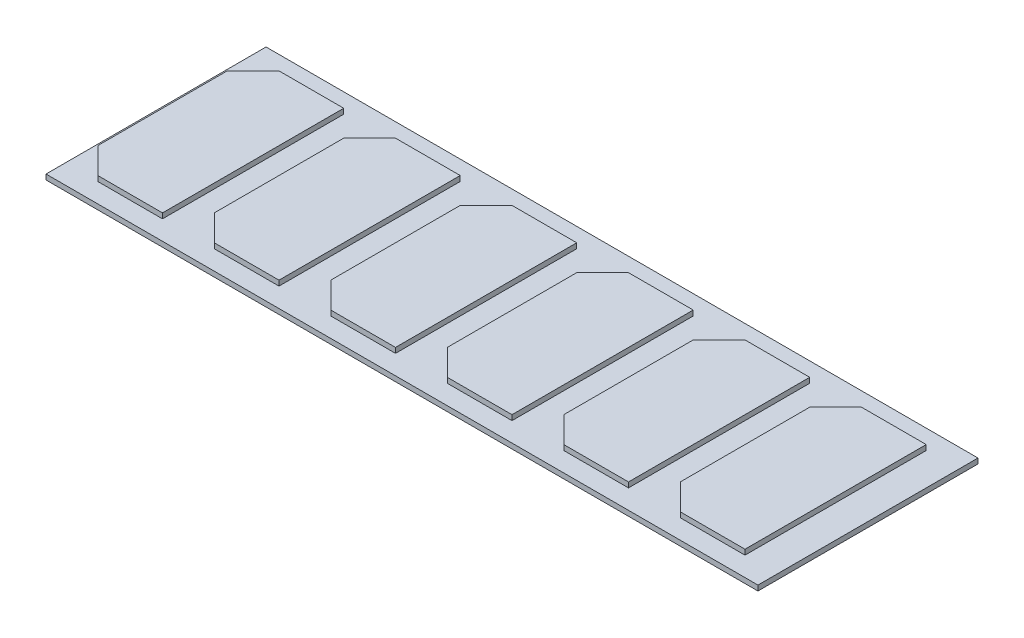
SolidWorks part; units mm, degrees
ref_plane "Front Plane" through (0, 0, 0) normal (0, 0, 1) x (1, 0, 0)
ref_plane "Top Plane" through (0, 0, 0) normal (0, 1, 0) x (1, 0, 0)
ref_plane "Right Plane" through (0, 0, 0) normal (1, 0, 0) x (0, 0, -1)
sketch "Sketch1" plane through (0, 0, 0) normal (0, 1, 0) x (1, 0, 0)
  line L1 (-137.5, -42.5) -> (137.5, -42.5)
  line L2 (-137.5, -42.5) -> (-137.5, 42.5)
  line L3 (-137.5, 42.5) -> (137.5, 42.5)
  line L4 (137.5, -42.5) -> (137.5, 42.5)
  line L5 (-137.5, -42.5) -> (137.5, 42.5) construction
  line L6 (-137.5, 42.5) -> (137.5, -42.5) construction
  point P0 (0, 0)
  dimension "D1" = 275
  dimension "D2" = 85
extrude "Boss-Extrude1" add sketch "Sketch1" along normal blind 2
sketch "Sketch2" plane through (0, 2, 0) normal (0, 1, 0) x (1, 0, 0)
  line L0 (-100, 35) -> (-100, -35)
  line L1 (-100, -35) -> (-125, -35)
  line L2 (-125, -35) -> (-135, -25)
  line L3 (-135, -25) -> (-135, 25)
  line L4 (-135, 25) -> (-125, 35)
  line L5 (-125, 35) -> (-100, 35)
  line L6 (-186.987, 0) -> (-73.9541, 0) construction
  line L7 (-90, 25) -> (-80, 35)
  line L8 (-90, -25) -> (-90, 25)
  line L9 (-80, -35) -> (-90, -25)
  line L10 (-55, -35) -> (-80, -35)
  line L11 (-55, 35) -> (-55, -35)
  line L12 (-80, 35) -> (-55, 35)
  line L13 (-45, 25) -> (-35, 35)
  line L14 (-45, -25) -> (-45, 25)
  line L15 (-35, -35) -> (-45, -25)
  line L16 (-10, -35) -> (-35, -35)
  line L17 (-10, 35) -> (-10, -35)
  line L18 (-35, 35) -> (-10, 35)
  line L19 (0, 25) -> (10, 35)
  line L20 (0, -25) -> (0, 25)
  line L21 (10, -35) -> (0, -25)
  line L22 (35, -35) -> (10, -35)
  line L23 (35, 35) -> (35, -35)
  line L24 (10, 35) -> (35, 35)
  line L25 (45, 25) -> (55, 35)
  line L26 (45, -25) -> (45, 25)
  line L27 (55, -35) -> (45, -25)
  line L28 (80, -35) -> (55, -35)
  line L29 (80, 35) -> (80, -35)
  line L30 (55, 35) -> (80, 35)
  line L31 (90, 25) -> (100, 35)
  line L32 (90, -25) -> (90, 25)
  line L33 (100, -35) -> (90, -25)
  line L34 (125, -35) -> (100, -35)
  line L35 (125, 35) -> (125, -35)
  line L36 (100, 35) -> (125, 35)
  point P12 (-100, 0)
  point P13 (-135, 0)
  dimension "D1" = 25
  dimension "D2" = 35
  dimension "D3" = 70
  dimension "D4" = 100
  dimension "D5" = 50
  dimension "D6" = 6
extrude "Boss-Extrude2" add sketch "Sketch2" along normal blind 2
